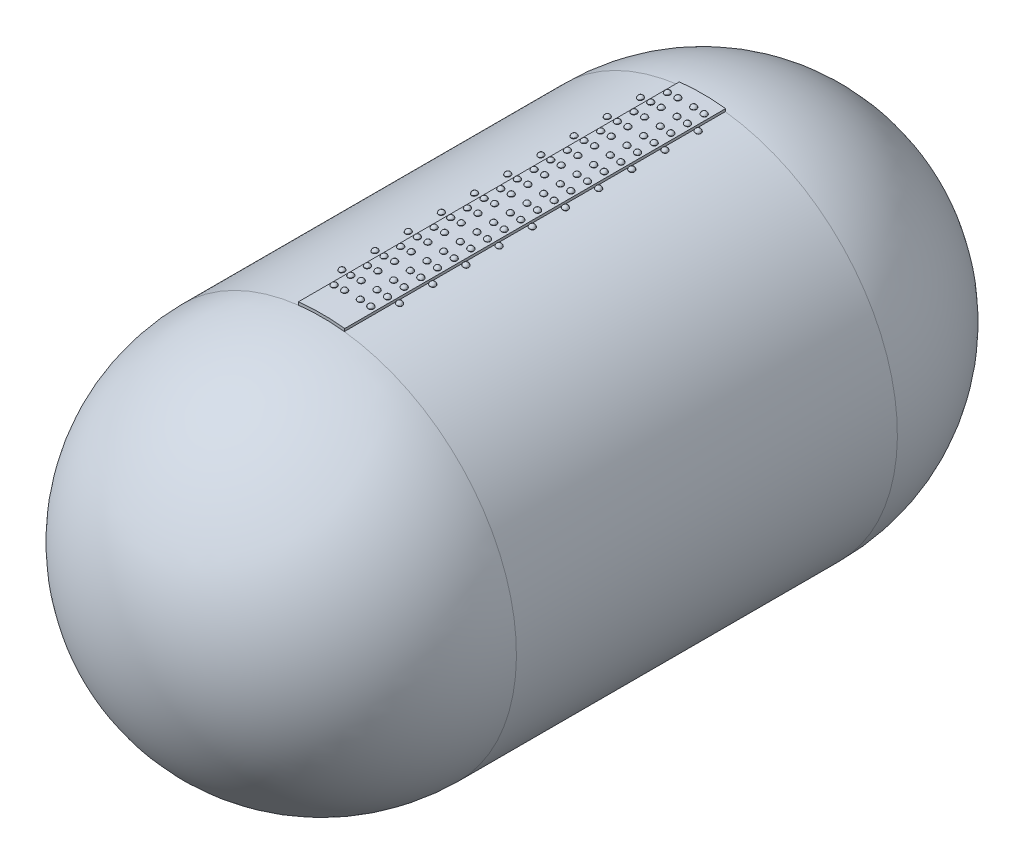
SolidWorks part; units mm, degrees
ref_plane "Front Plane" through (0, 0, 0) normal (0, 0, 1) x (1, 0, 0)
ref_plane "Top Plane" through (0, 0, 0) normal (0, 1, 0) x (1, 0, 0)
ref_plane "Right Plane" through (0, 0, 0) normal (1, 0, 0) x (0, 0, -1)
sketch "Sketch1" plane through (0, 0, 0) normal (0, 0, 1) x (1, 0, 0)
  line L0 (0, 0) -> (0, 860.5105) construction
  line L1 (-145.8317, 1237.4365) -> (-143.7249, 1219.5602)
  line L2 (145.8317, 1237.4365) -> (143.7249, 1219.5602)
  circle A0 centre (0, 0) radius 1228
  circle A1 centre (0, 0) radius 1200
  arc A2 (145.8317, 1237.4365) -> (-145.8317, 1237.4365) centre (0, 0) ccw
  point P7 (0, 1246)
  dimension "D" = 2400
  dimension "t" = 28
  dimension "outer_strap_thick" = 18
  dimension "right_half_width_of_outer_strap" = 146.1667
  dimension "half_width_outer_strap" = 146.1667
extrude "Boss-Extrude1" add sketch "Sketch1" along normal blind 2400
sketch "Sketch2" plane through (0, 0, 0) normal (0, 0, 1) x (1, 0, 0)
  line L0 (0, 0) -> (-49.487, 1245.0169) construction
  line L1 (0, 0) -> (49.487, 1245.0169) construction
  line L2 (-49.487, 1245.0169) -> (-24.6691, 620.636) construction
  line L3 (0, 0) -> (115.3347, 1240.6506) construction
  line L5 (0, 0) -> (88.9118, 606.0572) construction
  arc A0 (145.8317, 1237.4365) -> (-145.8317, 1237.4365) centre (0, 0) ccw construction
  arc A4 (145.8317, 1237.4365) -> (-145.8317, 1237.4365) centre (0, 0) ccw construction
  point P0 (49.487, 1245.0169)
  point P1 (-49.487, 1245.0169)
  point P5 (0, 1246)
  point P9 (180.8588, 1232.8042)
  point P13 (115.3347, 1240.6506)
  dimension "row1_rytdist_from_center" = 49.5
  dimension "row_2_rytdist_from_center" = 49.5
  dimension "outerinner pitch" = 66
  dimension "2nd_row_and_3rd_row_dist" = 66
ref_plane "Plane1" through (-49.487, 1245.0169, 0) normal (-0.0397, 0.9992, 0) x (0.9992, 0.0397, 0)
sketch "Sketch3" plane through (-49.487, 1245.0169, 0) normal (-0.0397, 0.9992, 0) x (0.9992, 0.0397, 0)
  line L0 (0, 0) -> (0, -2684.229) construction
ref_plane "Plane2" through (0, 0, 105) normal (0, 0, 1) x (1, 0, 0)
sketch "Sketch4" plane through (0, 0, 105) normal (0, 0, 1) x (1, 0, 0)
  line L0 (-49.487, 1245.0169) -> (-28.5161, 717.4227) construction
  line L1 (0, 0) -> (-49.487, 1245.0169) construction
  line L2 (-49.487, 1245.0169) -> (-65.974, 1244.3616)
  line L3 (499.9182, 1266.8547) -> (-598.8921, 1223.1791) construction
  line L4 (-65.974, 1244.3616) -> (-68.5175, 1248.3887)
  line L5 (-68.5175, 1248.3887) -> (-49.6508, 1249.1386)
  line L6 (-49.6508, 1249.1386) -> (-49.487, 1245.0169)
  dimension "rvt_rad" = 16.5
  dimension "taper_height" = 4.125
  dimension "taper_angle" = 120
revolve "Revolve1" add sketch "Sketch4" angle 360 about L0
sketch "Sketch6" plane through (0, 0, 105) normal (0, 0, 1) x (1, 0, 0)
  line L0 (-49.487, 1245.0169) -> (-24.6691, 620.636) construction
  line L1 (-30.7841, 1249.8885) -> (-68.5175, 1248.3887) construction
  line L2 (-32.5568, 1246.5155) -> (-66.4827, 1245.167) construction
  line L3 (-68.5175, 1248.3887) -> (-65.974, 1244.3616) construction
  line L4 (-33, 1245.6722) -> (-30.7841, 1249.8885) construction
  line L6 (-49.6508, 1249.1386) -> (-50.281, 1264.9939)
  line L7 (-49.6508, 1249.1386) -> (-68.5175, 1248.3887)
  line L8 (-49.5197, 1245.8412) -> (-24.3299, 612.1031) construction
  arc A0 (-68.5175, 1248.3887) -> (-50.281, 1264.9939) centre (-49.5197, 1245.8412) cw
  point P0 (-49.5197, 1245.8412)
  point P11 (-49.5197, 1245.8412)
  point P15 (-49.5197, 1245.8412)
  dimension "arc_center_dist" = 3.3
revolve "Revolve2" add sketch "Sketch6" angle 360 about L6
mirror "Mirror1" about plane through (0, 0, 0) normal (1, 0, 0) of bodies 103
pattern_linear "LPattern1" count 21 spacing 105 along (0, 0, 1) of bodies 103
pattern_linear "LPattern2" count 21 spacing 105 along (0, 0, 1) of bodies 104
sketch "Sketch7" plane through (0, 0, 0) normal (1, 0, 0) x (0, 0, -1)
  line L0 (0, 0) -> (0, -1228)
  line L2 (0, 0) -> (1228, 0)
  line L3 (0, -1228) -> (0, 1219.5602) construction
  arc A0 (0, -1228) -> (1228, 0) centre (0, 0) ccw
revolve "Revolve3" add sketch "Sketch7" angle 360 about L2
ref_plane "Plane3" through (0, 0, 1200) normal (0, 0, 1) x (1, 0, 0)
mirror "Mirror2" about plane through (0, 0, 1200) normal (0, 0, 1) of "Revolve3"
ref_plane "Plane4" through (115.3347, 1240.6506, 0) normal (0.0926, 0.9957, 0) x (0.9957, -0.0926, 0)
sketch "Sketch8" plane through (115.3347, 1240.6506, 0) normal (0.0926, 0.9957, 0) x (0.9957, -0.0926, 0)
  line L0 (0, 0) -> (0, -3024.3198) construction
ref_plane "Plane5" through (0, 0, 105) normal (0, 0, 1) x (1, 0, 0)
sketch "Sketch9" plane through (0, 0, 105) normal (0, 0, 1) x (1, 0, 0)
  line L0 (115.3347, 1240.6506) -> (98.9055, 1242.1779)
  line L1 (691.5929, 1187.0799) -> (-460.9236, 1294.2213) construction
  line L2 (98.9055, 1242.1779) -> (96.916, 1246.5056)
  line L3 (115.3347, 1240.6506) -> (115.7165, 1244.7579)
  line L4 (115.7165, 1244.7579) -> (96.916, 1246.5056)
  dimension "rvt_dia" = 16.5
  dimension "taper_angle" = 120
  dimension "taper_height" = 4.125
revolve "Revolve4" add sketch "Sketch9" angle 360 about L3
sketch "Sketch11" plane through (0, 0, 105) normal (0, 0, 1) x (1, 0, 0)
  line L0 (132.3145, 1239.9007) -> (98.5076, 1243.0435) construction
  line L1 (96.916, 1246.5056) -> (98.9055, 1242.1779) construction
  line L2 (691.5929, 1187.0799) -> (-460.9236, 1294.2213) construction
  line L3 (134.517, 1243.0101) -> (96.916, 1246.5056) construction
  line L4 (131.7638, 1239.1233) -> (134.517, 1243.0101) construction
  line L5 (0, 0) -> (115.3347, 1240.6506) construction
  line L6 (115.7165, 1244.7579) -> (117.1853, 1260.5575)
  line L7 (115.7165, 1244.7579) -> (96.916, 1246.5056)
  arc A0 (96.916, 1246.5056) -> (117.1853, 1260.5575) centre (115.411, 1241.4721) cw
  point P0 (115.411, 1241.4721)
  point P6 (115.411, 1241.4721)
  dimension "center_arc_dist" = 3.3
revolve "Revolve5" add sketch "Sketch11" angle 360 about L6
mirror "Mirror3" about plane through (0, 0, 0) normal (1, 0, 0) of bodies 122
pattern_linear "LPattern3" count 21 spacing 105 along (0, 0, 1) of bodies 122
pattern_linear "LPattern4" count 21 spacing 105 along (0, 0, 1) of bodies 123
ref_plane "Plane7" through (0, 0, 209) normal (0, 0, 1) x (1, 0, 0)
ref_plane "Plane8" through (180.8588, 1232.8042, 0) normal (0.1452, 0.9894, 0) x (0.9894, -0.1452, 0)
sketch "Sketch15" plane through (180.8588, 1232.8042, 0) normal (0.1452, 0.9894, 0) x (0.9894, -0.1452, 0)
  line L0 (0, 0) -> (0, -2884.1025) construction
sketch "Sketch16" plane through (0, 0, 209) normal (0, 0, 1) x (1, 0, 0)
  line L0 (180.8588, 1232.8042) -> (164.5336, 1235.1992)
  line L1 (770.5499, 1146.2934) -> (-408.8322, 1319.3149) construction
  line L2 (164.5336, 1235.1992) -> (162.776, 1239.6262)
  line L3 (162.776, 1239.6262) -> (181.4576, 1236.8855)
  line L4 (0, 0) -> (88.9118, 606.0572) construction
  line L5 (181.4576, 1236.8855) -> (180.8588, 1232.8042)
  dimension "rvt_rad" = 16.5
  dimension "taper_angle" = 120
  dimension "taper_height" = 4.125
revolve "Revolve6" add sketch "Sketch16" angle 360 about L5
sketch "Sketch17" plane through (0, 0, 209) normal (0, 0, 1) x (1, 0, 0)
  line L2 (0, 0) -> (88.9118, 606.0572) construction
  line L3 (197.7751, 1231.1563) -> (164.182, 1236.0846) construction
  line L4 (162.776, 1239.6262) -> (164.5336, 1235.1992) construction
  line L5 (200.1392, 1234.1448) -> (162.776, 1239.6262) construction
  line L6 (164.5336, 1235.1992) -> (197.1841, 1230.4092) construction
  line L7 (183.7608, 1252.5852) -> (181.4576, 1236.8855)
  line L8 (181.4576, 1236.8855) -> (162.776, 1239.6262)
  arc A1 (162.776, 1239.6262) -> (183.7608, 1252.5852) centre (180.9786, 1233.6204) cw
  point P0 (180.9786, 1233.6204)
  point P10 (180.9786, 1233.6204)
  dimension "arc_center_dist" = 3.3
revolve "Revolve7" add sketch "Sketch17" angle 360 about L2
mirror "Mirror4" about plane through (0, 0, 0) normal (1, 0, 0) of bodies 137 136
pattern_linear "LPattern5" count 10 spacing 209 along (0, 0, 1) of bodies 136 137
pattern_linear "LPattern6" count 10 spacing 209 along (0, 0, 1) of bodies 157 138
